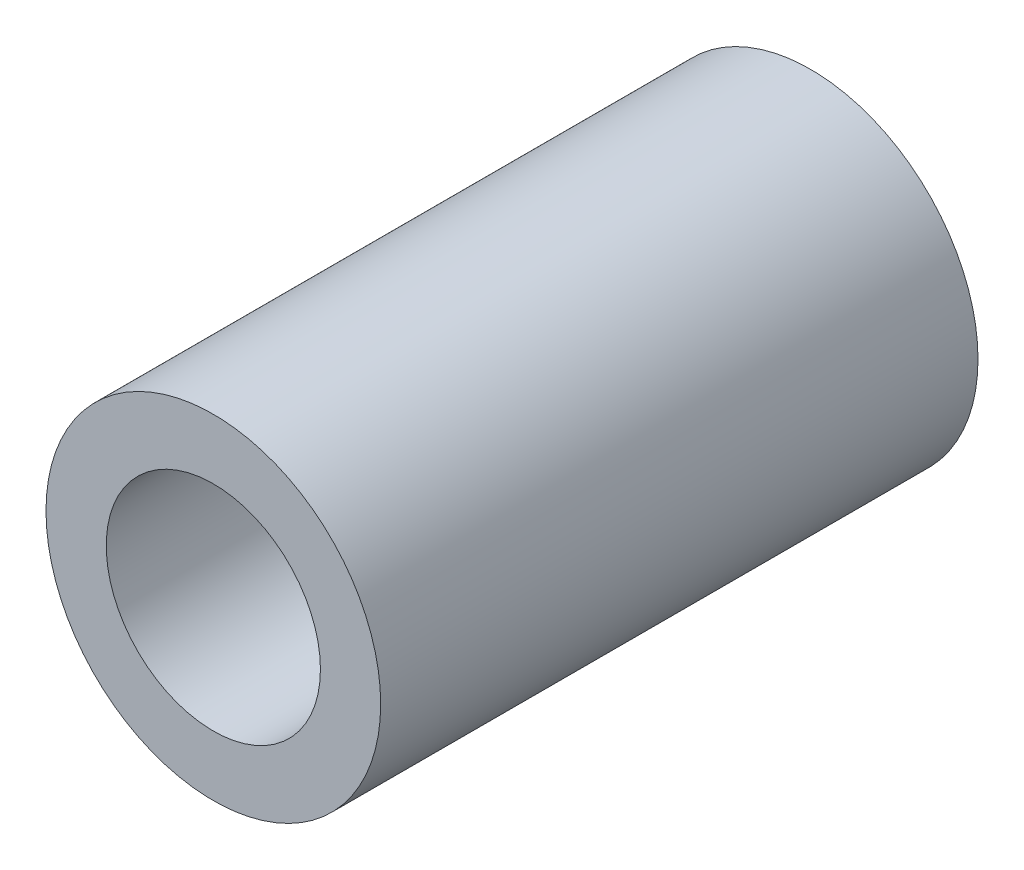
SolidWorks part; units mm, degrees
ref_plane "Front Plane" through (0, 0, 0) normal (0, 0, 1) x (1, 0, 0)
ref_plane "Top Plane" through (0, 0, 0) normal (0, 1, 0) x (1, 0, 0)
ref_plane "Right Plane" through (0, 0, 0) normal (1, 0, 0) x (0, 0, -1)
sketch "Sketch1" plane through (0, 0, 0) normal (0, 0, 1) x (1, 0, 0)
  circle A0 centre (0, 0) radius 3.048
  circle A1 centre (0, 0) radius 4.7625
  dimension "D1" = 9.525
  dimension "D2" = 6.096
extrude "Boss-Extrude1" add sketch "Sketch1" along normal blind 17
